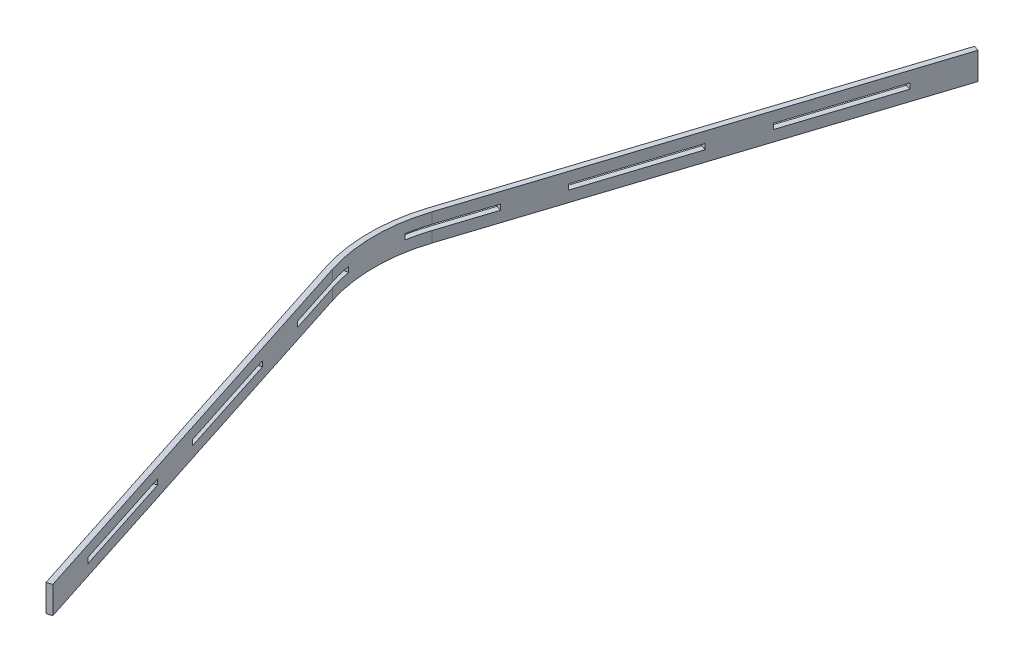
SolidWorks part; units mm, degrees
ref_plane "Front Plane" through (0, 0, 0) normal (0, 0, 1) x (1, 0, 0)
ref_plane "Top Plane" through (0, 0, 0) normal (0, 1, 0) x (1, 0, 0)
ref_plane "Right Plane" through (0, 0, 0) normal (1, 0, 0) x (0, 0, -1)
sketch "Sketch2" plane through (0, 0, 0) normal (0, 1, 0) x (1, 0, 0)
  line L0 (-295.0403, 95.1378) -> (-34.5174, 903.069) construction
  line L1 (-25, 910) -> (25, 910) construction
  line L2 (0, 0) -> (0, 979.251) construction
  line L3 (-181.6808, 251.1814) -> (-9.5174, 785.0928) construction
  line L4 (295.0403, 95.1378) -> (32.2825, 910) construction
  line L5 (181.6808, 251.1814) -> (9.5174, 785.0928) construction
  line L8 (-591.5307, 0) -> (570.3863, 0) construction
  line L9 (181.6808, -251.1814) -> (9.5174, -785.0928) construction
  line L10 (295.0403, -95.1378) -> (32.2825, -910) construction
  line L11 (-181.6808, -251.1814) -> (-9.5174, -785.0928) construction
  line L12 (-25, -910) -> (25, -910) construction
  line L13 (-295.0403, -95.1378) -> (-34.5174, -903.069) construction
  circle A0 centre (0, 0) radius 250 construction
  arc A1 (181.6808, 251.1814) -> (-181.6808, 251.1814) centre (0, 0) ccw construction
  arc A2 (-9.5174, 785.0928) -> (9.5174, 785.0928) centre (0, 782.0238) cw construction
  arc A3 (-295.0403, 95.1378) -> (-295.0403, -95.1378) centre (0, 0) ccw construction
  arc A4 (-25, 910) -> (-34.5174, 903.069) centre (-25, 900) ccw construction
  arc A5 (25, 910) -> (34.5174, 903.069) centre (25, 900) cw construction
  arc A22 (25, -910) -> (34.5174, -903.069) centre (25, -900) ccw construction
  arc A23 (-25, -910) -> (-34.5174, -903.069) centre (-25, -900) cw construction
  arc A24 (-9.5174, -785.0928) -> (9.5174, -785.0928) centre (0, -782.0238) ccw construction
  arc A25 (181.6808, -251.1814) -> (-181.6808, -251.1814) centre (0, 0) cw construction
  arc A26 (-181.6808, -251.1814) -> (181.6808, -251.1814) centre (0, 0) ccw construction
  arc A27 (295.0403, -95.1378) -> (295.0403, 95.1378) centre (0, 0) ccw construction
  point P15 (0, 814.6081)
  point P17 (-32.2825, 910)
  point P21 (0, 910)
  point P69 (0, -910)
  dimension "D1" = 500
  dimension "D2" = 10
  dimension "D3" = 10
  dimension "D8" = 60
  dimension "D9" = 910
  dimension "D11" = 50
sketch "Sketch3" plane through (0, 0, 0) normal (0, 1, 0) x (1, 0, 0)
  line L0 (-49.5235, -856.5322) -> (-40.0061, -853.4632)
  line L2 (-40.0061, -853.4632) -> (-285.5229, -92.0688) construction
  line L3 (-496.7261, 0) -> (519.5681, 0) construction
  line L4 (-49.5235, -856.5322) -> (-295.0403, -95.1378) construction
  line L5 (-70.6957, -758.2889) -> (-80.2131, -761.3579)
  line L6 (-132.0749, -567.9403) -> (-141.5923, -571.0093)
  line L7 (-162.7645, -472.766) -> (-172.2819, -475.835)
  line L8 (0, 1168.7659) -> (0, -1304.5967) construction
  line L9 (-233.6611, -285.4864) -> (-224.1437, -282.4174)
  line L10 (-264.3507, -190.3121) -> (-254.8333, -187.2431)
  line L11 (-305.2904, -53.8309) -> (-295.4423, -52.0945)
  line L12 (-285.5229, -92.0688) -> (-254.8333, -187.2431) construction
  line L13 (-295.0403, -95.1378) -> (-264.3507, -190.3121) construction
  line L14 (-141.5923, -571.0093) -> (-172.2819, -475.835)
  line L15 (-224.1437, -282.4174) -> (-162.7645, -472.766) construction
  line L16 (-172.2819, -475.835) -> (-233.6611, -285.4864) construction
  line L17 (-80.2131, -761.3579) -> (-141.5923, -571.0093) construction
  line L18 (-132.0749, -567.9403) -> (-70.6957, -758.2889) construction
  line L19 (-162.7645, -472.766) -> (-132.0749, -567.9403)
  line L20 (-80.2131, -761.3579) -> (-49.5235, -856.5322)
  line L21 (-70.6957, -758.2889) -> (-40.0061, -853.4632)
  line L22 (-264.3507, -190.3121) -> (-233.6611, -285.4864)
  line L23 (-254.8333, -187.2431) -> (-224.1437, -282.4174)
  line L24 (-132.0749, 567.9403) -> (-70.6957, 758.2889) construction
  line L25 (-80.2131, 761.3579) -> (-141.5923, 571.0093) construction
  line L26 (-172.2819, 475.835) -> (-233.6611, 285.4864) construction
  line L27 (-224.1437, 282.4174) -> (-162.7645, 472.766) construction
  line L28 (-295.0403, 95.1378) -> (-264.3507, 190.3121) construction
  line L29 (-285.5229, 92.0688) -> (-254.8333, 187.2431) construction
  line L30 (-49.5235, 856.5322) -> (-295.0403, 95.1378) construction
  line L31 (-40.0061, 853.4632) -> (-285.5229, 92.0688) construction
  line L32 (-254.8333, 187.2431) -> (-224.1437, 282.4174)
  line L33 (-264.3507, 190.3121) -> (-233.6611, 285.4864)
  line L34 (-70.6957, 758.2889) -> (-40.0061, 853.4632)
  line L35 (-80.2131, 761.3579) -> (-49.5235, 856.5322)
  line L36 (0, -1168.7659) -> (0, 1304.5967) construction
  line L37 (-162.7645, 472.766) -> (-132.0749, 567.9403)
  line L38 (-141.5923, 571.0093) -> (-172.2819, 475.835)
  line L39 (-305.2904, 53.8309) -> (-295.4423, 52.0945)
  line L40 (-264.3507, 190.3121) -> (-254.8333, 187.2431)
  line L41 (-233.6611, 285.4864) -> (-224.1437, 282.4174)
  line L42 (-162.7645, 472.766) -> (-172.2819, 475.835)
  line L43 (-132.0749, 567.9403) -> (-141.5923, 571.0093)
  line L44 (-70.6957, 758.2889) -> (-80.2131, 761.3579)
  line L45 (-49.5235, 856.5322) -> (-40.0061, 853.4632)
  line L64 (-295.0403, -95.1378) -> (-34.5174, -903.069) construction
  arc A0 (-285.5229, 92.0688) -> (-285.5229, -92.0688) centre (0, 0) ccw construction
  arc A1 (-295.0403, 95.1378) -> (-295.0403, -95.1378) centre (0, 0) ccw construction
  arc A2 (-295.0403, 95.1378) -> (-295.0403, -95.1378) centre (0, 0) ccw construction
  arc A3 (-295.4423, -52.0945) -> (-285.5229, -92.0688) centre (0, 0) ccw construction
  arc A4 (-305.2904, -53.8309) -> (-295.0403, -95.1378) centre (0, 0) ccw construction
  arc A5 (-295.4423, -52.0945) -> (-295.4423, 52.0945) centre (0, 0) cw
  arc A6 (-305.2904, -53.8309) -> (-305.2904, 53.8309) centre (0, 0) cw
  arc A7 (-305.2904, 53.8309) -> (-295.0403, 95.1378) centre (0, 0) cw construction
  arc A8 (-295.4423, 52.0945) -> (-285.5229, 92.0688) centre (0, 0) cw construction
  dimension "D8" = 10
  dimension "D1" = 10
  dimension "D2" = 800
  dimension "D3" = 100
  dimension "D4" = 200
  dimension "D5" = 100
  dimension "D6" = 200
  dimension "D7" = 100
extrude "Boss-Extrude1" add sketch "Sketch3" along normal mid plane 10
sketch "Sketch4" plane through (0, 5, 0) normal (0, 1, 0) x (1, 0, 0)
  line L0 (-49.5235, 856.5322) -> (-40.0061, 853.4632)
  line L1 (-40.0061, 853.4632) -> (-285.5229, 92.0688)
  line L2 (-49.5235, 856.5322) -> (-295.0403, 95.1378)
  line L3 (-591.5307, 0) -> (570.3863, 0) construction
  line L4 (-49.5235, -856.5322) -> (-295.0403, -95.1378)
  line L5 (-40.0061, -853.4632) -> (-285.5229, -92.0688)
  line L6 (-49.5235, -856.5322) -> (-40.0061, -853.4632)
  arc A0 (-285.5229, -92.0688) -> (-285.5229, 92.0688) centre (0, 0) cw
  arc A2 (-295.0403, -95.1378) -> (-295.0403, 95.1378) centre (0, 0) cw
extrude "Boss-Extrude2" add sketch "Sketch4" along normal blind 20
sketch "Sketch5" plane through (0, -5, 0) normal (0, -1, 0) x (1, 0, 0)
  line L0 (-49.5235, 856.5322) -> (-40.0061, 853.4632)
  line L1 (-40.0061, 853.4632) -> (-285.5229, 92.0688)
  line L2 (-254.8333, 187.2431) -> (-285.5229, 92.0688) construction
  line L3 (-295.0403, 95.1378) -> (-34.5174, 903.069) construction
  line L4 (-295.0403, 95.1378) -> (-49.5235, 856.5322)
  line L5 (-591.5307, 0) -> (0, 0) construction
  line L6 (-295.0403, -95.1378) -> (-49.5235, -856.5322)
  line L7 (-40.0061, -853.4632) -> (-285.5229, -92.0688)
  line L8 (-49.5235, -856.5322) -> (-40.0061, -853.4632)
  arc A0 (-285.5229, -92.0688) -> (-285.5229, 92.0688) centre (0, 0) cw
  arc A2 (-295.0403, -95.1378) -> (-295.0403, 95.1378) centre (0, 0) cw
extrude "Boss-Extrude3" add sketch "Sketch5" along normal blind 20
